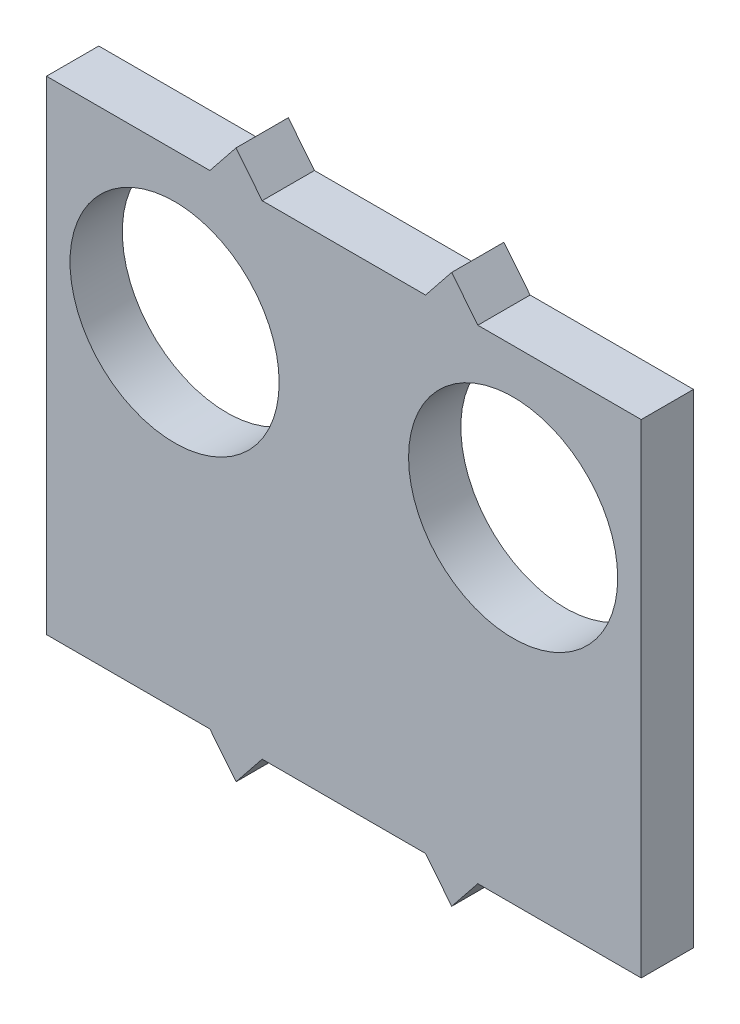
SolidWorks part; units mm, degrees
ref_plane "Front Plane" through (0, 0, 0) normal (0, 0, 1) x (1, 0, 0)
ref_plane "Top Plane" through (0, 0, 0) normal (0, 1, 0) x (1, 0, 0)
ref_plane "Right Plane" through (0, 0, 0) normal (1, 0, 0) x (0, 0, -1)
sketch "Sketch1" plane through (0, 0, 0) normal (0, 0, 1) x (1, 0, 0)
  line L0 (22.75, 37) -> (22.75, 14.7203) construction
  line L1 (0, 0) -> (45.5, 0)
  line L2 (0, 0) -> (0, 37)
  line L3 (0, 37) -> (45.5, 37)
  line L4 (45.5, 0) -> (45.5, 37)
  line L5 (12.5, 37) -> (14.5, 39.5)
  line L6 (14.5, 39.5) -> (16.5, 37)
  line L7 (31, 39.5) -> (29, 37)
  line L8 (33, 37) -> (31, 39.5)
  line L9 (0, 18.5) -> (57.9593, 18.5) construction
  line L10 (33, 0) -> (31, -2.5)
  line L11 (31, -2.5) -> (29, 0)
  line L12 (14.5, -2.5) -> (16.5, 0)
  line L13 (12.5, 0) -> (14.5, -2.5)
  point P9 (22.75, 37)
  point P16 (0, 18.5)
  point P17 (32, 38.25)
  point P18 (32, -1.25)
  dimension "D1" = 37
  dimension "D2" = 45.5
  dimension "D3" = 16.5
  dimension "D4" = 2.5
  dimension "D5" = 4
extrude "Basis" add sketch "Sketch1" along normal blind 4 contours L1 L4 L3 L2 | L6 L5 L3 | L3 L8 L7 | L1 L13 L12 | L11 L10 L1
sketch "Sketch2" [suppressed] plane through (0, 0, 4) normal (0, 0, 1) x (1, 0, 0)
  line L0 (16.5, 37) -> (29, 37) construction
  circle A0 centre (22.75, 23) radius 6.8
  point P5 (22.75, 37)
  dimension "D1" = 13.6
  dimension "D2" = 14
extrude "Camera gat " [suppressed] cut sketch "Sketch2" against normal up to surface (4 mm away)
sketch "Sketch5" [suppressed] plane through (0, 0, 4) normal (0, 0, 1) x (1, 0, 0)
  line L0 (8.6574, 7.1957) -> (36.8426, 7.1957) construction
  line L1 (16.5, 37) -> (29, 37) construction
  text T0 "camera" font "Yu Gothic UI Semilight" height 3.5
  point P2 (22.75, 7.1957)
  point P5 (22.75, 37)
extrude "Cut-Extrude4" [suppressed] cut sketch "Sketch5" against normal blind 0.2
sketch "Sketch3" plane through (0, 0, 4) normal (0, 0, 1) x (1, 0, 0)
  line L0 (22.75, 37) -> (22.75, 0) construction
  line L1 (16.5, 37) -> (29, 37) construction
  line L2 (16.5, 0) -> (29, 0) construction
  line L3 (0, 37) -> (12.5, 37) construction
  circle A0 centre (9.8, 25.6) radius 8
  circle A1 centre (35.7, 25.6) radius 8
  dimension "D3" = 16
  dimension "D1" = 11.4
  dimension "D2" = 25.9
extrude "HR04 gat " cut sketch "Sketch3" against normal up to surface (4 mm away) up to face at (22.75, 18.5, 0)
sketch "Sketch4" [suppressed] plane through (0, 0, 4) normal (0, 0, 1) x (1, 0, 0)
  line L0 (7.7992, 12.9938) -> (37.7008, 12.9938) construction
  line L1 (16.5, 37) -> (29, 37) construction
  text T0 "AFSTAND SENSOR" font "Yu Gothic UI Semilight" height 3.5
  point P5 (22.75, 12.9938)
  point P8 (22.75, 37)
extrude "Afstand sensor" [suppressed] cut sketch "Sketch4" against normal blind 0.2
sketch "Sketch6" [suppressed] plane through (0, 0, 4) normal (0, 0, 1) x (1, 0, 0)
  line L4 (16.5, 37) -> (29, 37) construction
  point P0 (22.75, 31.8)
  point P3 (22.75, 37)
  line B0 (9.1, 31.8) -> (36.4, 31.8)
  line B1 (9.1, 31.8) -> (9.1, 16.3191)
  line B2 (9.1, 16.3191) -> (36.4, 16.3191)
  line B3 (36.4, 31.8) -> (36.4, 16.3191)
  circle B4 centre (11.1, 34.0981) radius 1.5
  circle B5 centre (34.4, 34.0981) radius 1.5
  circle B6 centre (34.4, 10.2981) radius 1.5
  circle B7 centre (11.1, 10.2981) radius 1.5
  dimension "D1" = 5.2
sketch_block_instance "Block1-1" [suppressed]
sketch_block "Block1" parameters "D1"=3, "D2"=3, "D3"=3, "D4"=3
extrude "Cut-Extrude5" [suppressed] cut sketch "Sketch6" against normal up to surface (4 mm away)
sketch "Sketch7" [suppressed] plane through (0, 0, 4) normal (0, 0, 1) x (1, 0, 0)
  line L0 (-2.0092, 11.0348) -> (47.5092, 11.0348) construction
  line L1 (16.5, 37) -> (29, 37) construction
  text T0 "oled scherm " font "Yu Gothic UI Semilight" height 3.5
  point P4 (22.75, 37)
  point P5 (22.75, 11.0348)
extrude "Cut-Extrude6" [suppressed] cut sketch "Sketch7" against normal blind 0.2
